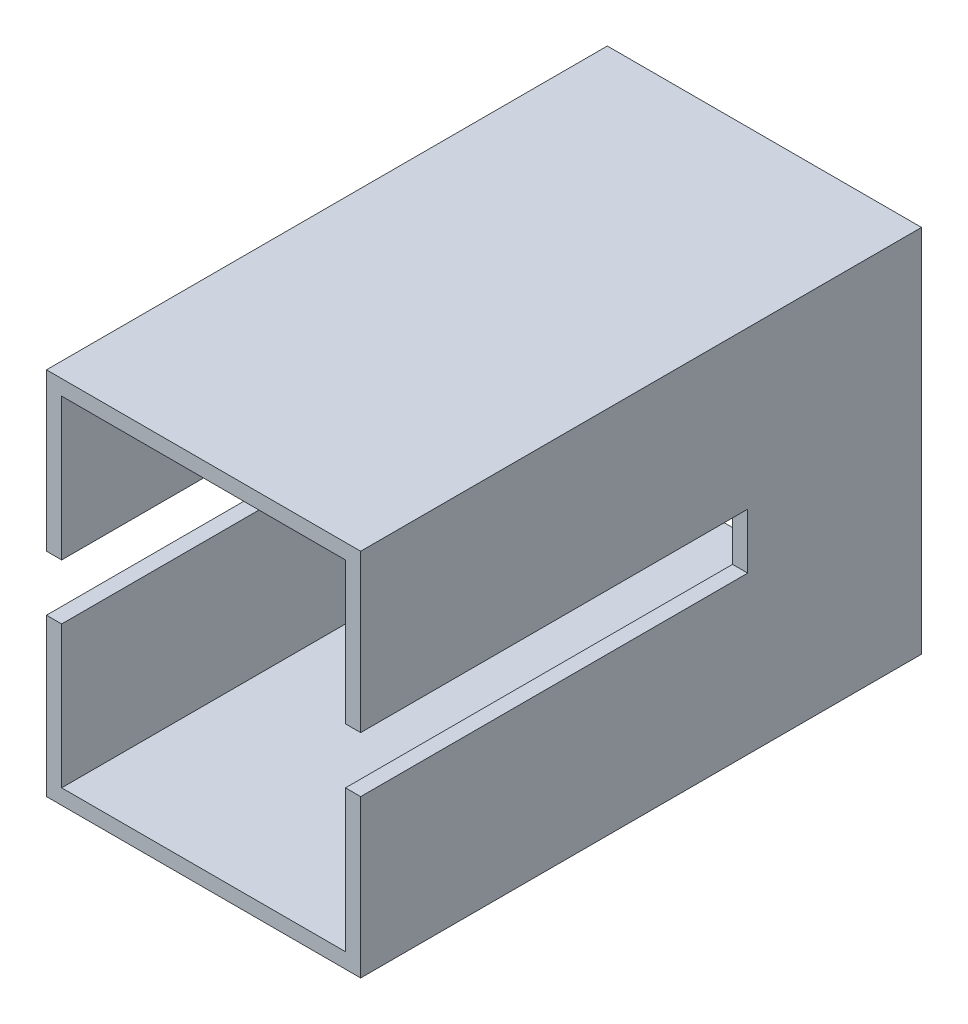
SolidWorks part; units mm, degrees
ref_plane "Ebene vorne" through (0, 0, 0) normal (0, 0, 1) x (1, 0, 0)
ref_plane "Ebene oben" through (0, 0, 0) normal (0, 1, 0) x (1, 0, 0)
ref_plane "Ebene rechts" through (0, 0, 0) normal (1, 0, 0) x (0, 0, -1)
sketch "Sketch3" plane through (0, 0, 0) normal (0, 0, 1) x (1, 0, 0)
  line L1 (-9.35, 11.175) -> (9.35, 11.175)
  line L2 (-9.35, 11.175) -> (-9.35, -11.175)
  line L3 (-9.35, -11.175) -> (9.35, -11.175)
  line L4 (9.35, 11.175) -> (9.35, -11.175)
  line L5 (-9.35, 11.175) -> (9.35, -11.175) construction
  line L6 (-9.35, -11.175) -> (9.35, 11.175) construction
  point P0 (0, 0)
  dimension "D1" = 18.7
  dimension "D2" = 22.35
extrude "Extrude-Thin1" add sketch "Sketch3" along normal blind 36.95 thin thin type one direction wall 1
sketch "Sketch4" plane through (-10.35, 0, 0) normal (-1, 0, 0) x (0, 0, 1)
  line L0 (36.95, 12.175) -> (36.95, -12.175) construction
  line L1 (11.45, 1.825) -> (36.95, 1.825)
  line L2 (11.45, 1.825) -> (11.45, -1.825)
  line L3 (11.45, -1.825) -> (36.95, -1.825)
  line L4 (36.95, 1.825) -> (36.95, -1.825)
  line L5 (11.45, 1.825) -> (36.95, -1.825) construction
  line L6 (11.45, -1.825) -> (36.95, 1.825) construction
  line L7 (0, 12.175) -> (0, -12.175) construction
  point P0 (24.2, 0)
  dimension "D1" = 11.45
  dimension "D2" = 3.65
extrude "Cut-Extrude1" cut sketch "Sketch4" against normal through all
